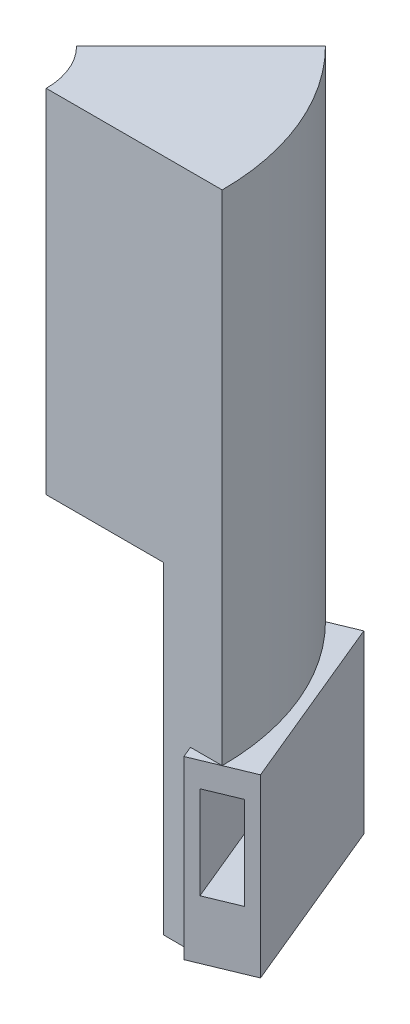
SolidWorks part; units mm, degrees
ref_plane "Front Plane" through (0, 0, 0) normal (0, 0, 1) x (1, 0, 0)
ref_plane "Top Plane" through (0, 0, 0) normal (0, 1, 0) x (1, 0, 0)
ref_plane "Right Plane" through (0, 0, 0) normal (1, 0, 0) x (0, 0, -1)
sketch "Sketch1" plane through (0, 0, 0) normal (0, 0, 1) x (1, 0, 0)
  line L0 (0, 0) -> (0, 60)
  line L1 (0, 60) -> (30, 60)
  line L2 (30, 60) -> (30, -55)
  line L3 (30, -55) -> (20, -55)
  line L4 (20, -55) -> (20, 0)
  line L5 (20, 0) -> (0, 0)
  line L6 (-12.5, 0) -> (-12.5, 41.9322) construction
  dimension "D1" = 60
  dimension "D2" = 55
  dimension "D3" = 20
  dimension "D4" = 10
  dimension "D5" = 12.5
revolve "Revolve1" add sketch "Sketch1" angle 45 about L6
ref_plane "Plane1" through (25.6066, 0, -10.6066) normal (-0.9239, 0, 0.3827) x (0.3827, 0, 0.9239)
sketch "Sketch2" plane through (25.6066, 0, -10.6066) normal (-0.9239, 0, 0.3827) x (0.3827, 0, 0.9239)
  line L0 (-21.0476, -55) -> (-21.0476, 60) construction
  line L1 (11.4805, -55) -> (-21.0476, -55)
  line L2 (11.4805, -55) -> (11.4805, -25)
  line L3 (11.4805, -25) -> (-21.0476, -25)
  line L4 (-21.0476, -55) -> (-21.0476, -25)
  dimension "D1" = 30
extrude "Boss-Extrude1" add sketch "Sketch2" against normal mid plane 10
sketch "Sketch3" plane through (4.3934, 0, 10.6066) normal (0.3827, 0, 0.9239) x (0.9239, 0, -0.3827)
  line L0 (27.7164, -55) -> (27.7164, -42.9465) construction
  line L1 (32.7164, -55) -> (22.7164, -55) construction
  line L3 (24.8164, -29.2) -> (30.6164, -29.2)
  line L4 (24.8164, -29.2) -> (24.8164, -45)
  line L5 (24.8164, -45) -> (30.6164, -45)
  line L6 (30.6164, -29.2) -> (30.6164, -45)
  line L7 (24.8164, -29.2) -> (30.6164, -45) construction
  line L8 (24.8164, -45) -> (30.6164, -29.2) construction
  point P4 (27.7164, -37.1)
  dimension "D1" = 10
  dimension "D3" = 5.8
  dimension "D4" = 15.8
extrude "Cut-Extrude1" cut sketch "Sketch3" against normal through all
